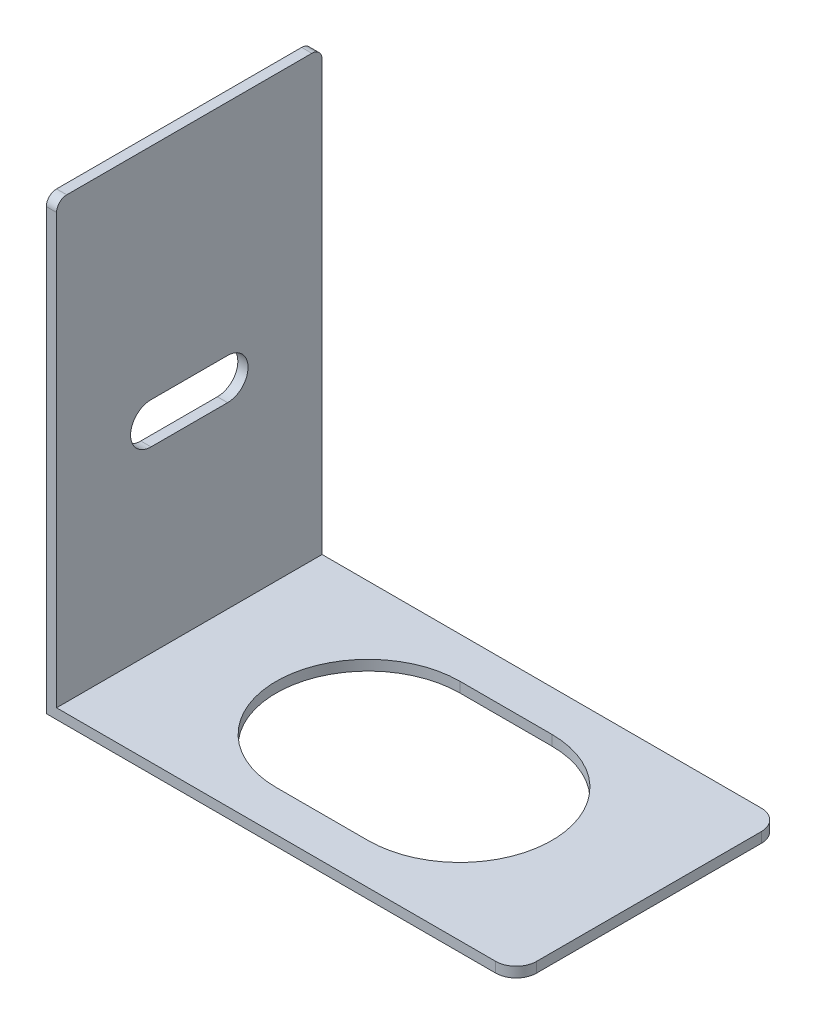
SolidWorks part; units mm, degrees
ref_plane "Front Plane" through (0, 0, 0) normal (0, 0, 1) x (1, 0, 0)
ref_plane "Top Plane" through (0, 0, 0) normal (0, 1, 0) x (1, 0, 0)
ref_plane "Right Plane" through (0, 0, 0) normal (1, 0, 0) x (0, 0, -1)
sketch "Sketch1" plane through (0, 0, 0) normal (0, 1, 0) x (1, 0, 0)
  line L0 (-4.5, 0) -> (4.5, 0) construction
  line L1 (-23, 13) -> (21, 13)
  line L2 (-23, 13) -> (-23, -13)
  line L3 (-23, -13) -> (21, -13)
  line L4 (23, 11) -> (23, -11)
  line L5 (-23, 13) -> (23, -13) construction
  line L6 (-23, -13) -> (23, 13) construction
  line L7 (-4.5, 9) -> (4.5, 9)
  line L8 (-4.5, -9) -> (4.5, -9)
  arc A0 (-4.5, 9) -> (-4.5, -9) centre (-4.5, 0) ccw
  arc A1 (4.5, -9) -> (4.5, 9) centre (4.5, 0) ccw
  arc A2 (21, -13) -> (23, -11) centre (21, -11) ccw
  arc A3 (21, 13) -> (23, 11) centre (21, 11) cw
  point P0 (0, 0)
  point P8 (0, 0)
  point P13 (0, 0)
  point P14 (0, 0)
  dimension "D3" = 9
  dimension "D5" = 2
  dimension "D1" = 26
  dimension "D2" = 46
  dimension "D4" = 9
extrude "Boss-Extrude1" add sketch "Sketch1" along normal blind 1
sketch "Sketch2" plane through (0, 1, 0) normal (0, 1, 0) x (1, 0, 0)
  line L0 (-23, 13) -> (-23, -13) construction
  line L1 (-23, 13) -> (-23, -13)
  line L2 (-23, -13) -> (-22, -13)
  line L3 (-23, -13) -> (21, -13) construction
  line L4 (-22, -13) -> (-22, 13)
  line L5 (21, 13) -> (-23, 13) construction
  line L6 (-22, 13) -> (-23, 13)
  dimension "D1" = 1
extrude "Boss-Extrude2" add sketch "Sketch2" along normal blind 43
sketch "Sketch3" plane through (-22, 0, 0) normal (1, 0, 0) x (0, 0, -1)
  line L0 (-13, 44) -> (13, 1) construction
  line L1 (-13, 22.5) -> (13, 22.5) construction
  line L4 (-13, 44) -> (-13, 1) construction
  line L5 (13, 44) -> (13, 1) construction
  line L6 (-3.75, 20.5) -> (3.75, 20.5) construction
  line L7 (-3.75, 22.5) -> (3.75, 22.5)
  line L8 (-3.75, 18.5) -> (3.75, 18.5)
  arc A0 (-3.75, 22.5) -> (-3.75, 18.5) centre (-3.75, 20.5) ccw
  arc A1 (3.75, 18.5) -> (3.75, 22.5) centre (3.75, 20.5) ccw
  point P12 (0, 20.5)
  point P17 (0, 22.5)
  point P18 (0, 0)
  dimension "D1" = 2
  dimension "D2" = 7.5
  dimension "D3" = 13
extrude "Cut-Extrude1" cut sketch "Sketch3" against normal blind 1
fillet "Fillet1" radius 1 2 edges at (-22.5, 44, 13) (-22.5, 44, -13)
